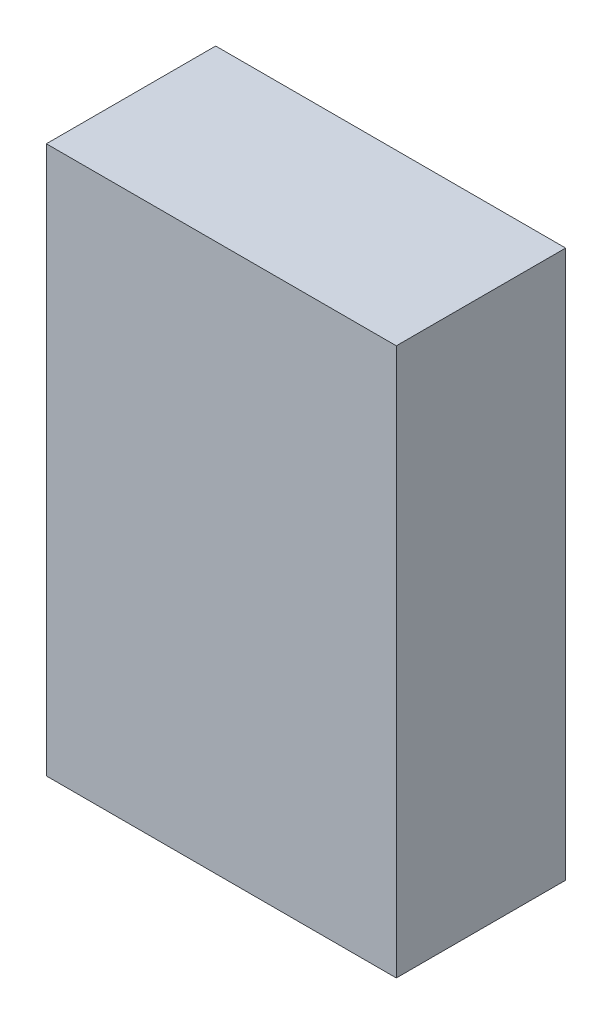
SolidWorks part; units mm, degrees
ref_plane "Plan de face" through (0, 0, 0) normal (0, 0, 1) x (1, 0, 0)
ref_plane "Plan de dessus" through (0, 0, 0) normal (0, 1, 0) x (1, 0, 0)
ref_plane "Plan de droite" through (0, 0, 0) normal (1, 0, 0) x (0, 0, -1)
sketch "Esquisse2" plane through (0, 0, 0) normal (0, 0, 1) x (1, 0, 0)
  line L1 (-31, 48.5) -> (31, 48.5)
  line L2 (-31, 48.5) -> (-31, -48.5)
  line L3 (-31, -48.5) -> (31, -48.5)
  line L4 (31, 48.5) -> (31, -48.5)
  line L5 (-31, 48.5) -> (31, -48.5) construction
  line L6 (-31, -48.5) -> (31, 48.5) construction
  point P0 (0, 0)
  dimension "D1" = 62
  dimension "D2" = 97
extrude "Boss.-Extru.1" add sketch "Esquisse2" along normal blind 30
